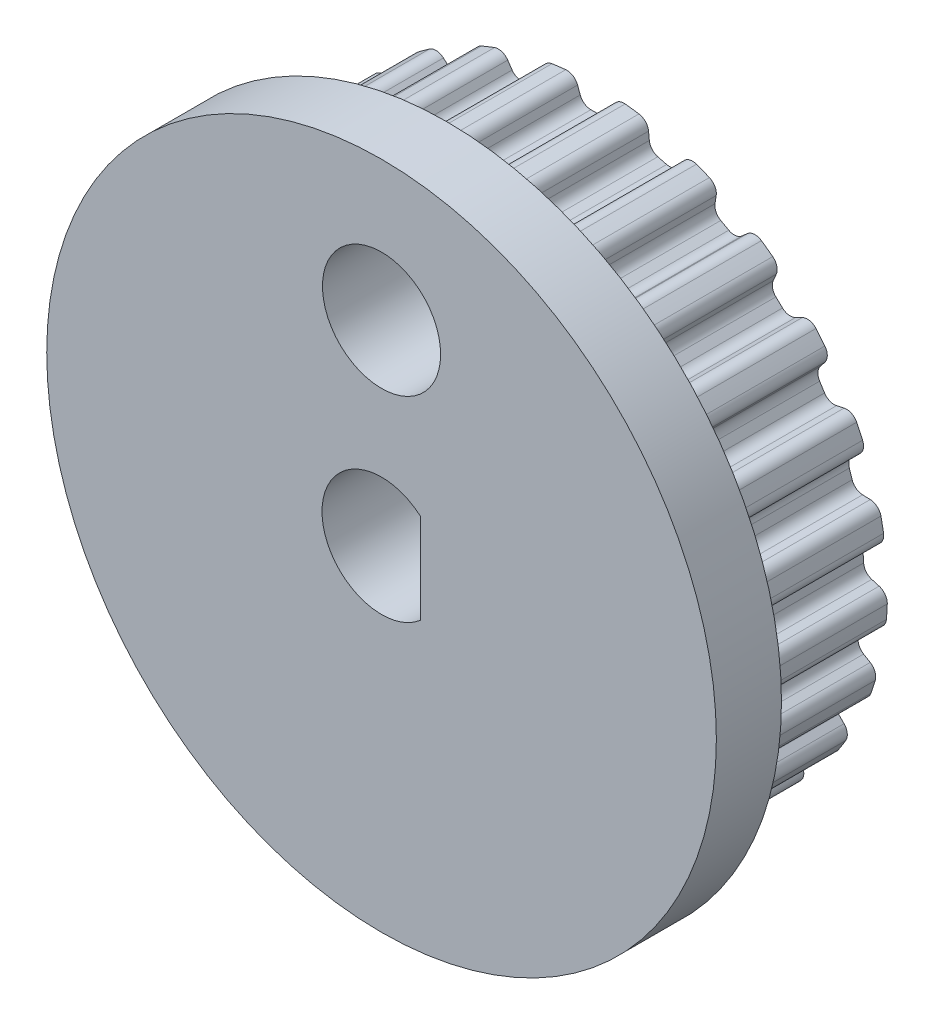
SolidWorks part; units mm, degrees
ref_plane "Front Plane" through (0, 0, 0) normal (0, 0, 1) x (1, 0, 0)
ref_plane "Top Plane" through (0, 0, 0) normal (0, 1, 0) x (1, 0, 0)
ref_plane "Right Plane" through (0, 0, 0) normal (1, 0, 0) x (0, 0, -1)
ref_plane "Plane1" through (0, 0, -5.3) normal (0, 0, -1) x (-1, 0, 0)
sketch "Sketch1" plane through (0, 0, -5.3) normal (0, 0, -1) x (-1, 0, 0)
  line L0 (-2.7705, -6.663) -> (-2.5415, -6.7537)
  line L1 (-2.3491, -7.0456) -> (-2.3549, -7.2528)
  line L2 (-1.4305, -7.4901) -> (-1.3357, -7.3057)
  line L3 (-1.0264, -7.1427) -> (-0.7821, -7.1735)
  line L4 (-0.5231, -7.4084) -> (-0.4772, -7.6106)
  line L5 (0.4772, -7.6106) -> (0.5231, -7.4084)
  line L6 (0.7821, -7.1735) -> (1.0264, -7.1427)
  line L7 (1.3357, -7.3057) -> (1.4305, -7.4901)
  line L8 (2.3549, -7.2528) -> (2.3491, -7.0456)
  line L9 (2.5415, -6.7537) -> (2.7705, -6.663)
  line L10 (3.1106, -6.744) -> (3.2483, -6.8991)
  line L11 (4.0846, -6.4393) -> (4.0274, -6.24)
  line L12 (4.1413, -5.9094) -> (4.3405, -5.7647)
  line L13 (4.6901, -5.7586) -> (4.862, -5.8745)
  line L14 (5.5576, -5.2212) -> (5.4527, -5.0424)
  line L15 (5.4808, -4.6939) -> (5.6377, -4.5041)
  line L16 (5.9748, -4.4113) -> (6.1701, -4.4808)
  line L17 (6.6815, -3.6751) -> (6.5354, -3.528)
  line L18 (6.4759, -3.1834) -> (6.5808, -2.9606)
  line L19 (6.8842, -2.7868) -> (7.0906, -2.8056)
  line L20 (7.3855, -1.898) -> (7.2075, -1.7918)
  line L21 (7.0641, -1.4729) -> (7.1103, -1.231)
  line L22 (7.3609, -0.9872) -> (7.5656, -0.9541)
  line L23 (7.6255, -0.0016) -> (7.4266, 0.0569)
  line L24 (7.2085, 0.3301) -> (7.193, 0.5759)
  line L25 (7.3752, 0.8744) -> (7.5652, 0.9574)
  line L26 (7.3864, 1.8948) -> (7.1792, 1.902)
  line L27 (6.8999, 2.1125) -> (6.8238, 2.3467)
  line L28 (6.9261, 2.681) -> (7.0894, 2.8087)
  line L29 (6.6831, 3.6722) -> (6.4806, 3.6277)
  line L30 (6.1578, 3.762) -> (6.0259, 3.9699)
  line L31 (6.0417, 4.3192) -> (6.1682, 4.4835)
  line L32 (5.5599, 5.2188) -> (5.3748, 5.1254)
  line L33 (5.0288, 5.1752) -> (4.8493, 5.3438)
  line L34 (4.7777, 5.6861) -> (4.8594, 5.8766)
  line L35 (4.0874, 6.4376) -> (3.9314, 6.301)
  line L36 (3.5837, 6.2632) -> (3.368, 6.3819)
  line L37 (3.2136, 6.6956) -> (3.2453, 6.9005)
  line L38 (2.358, 7.2518) -> (2.2409, 7.0807)
  line L39 (1.9136, 6.9577) -> (1.675, 7.0189)
  line L40 (1.4475, 7.2844) -> (1.4273, 7.4908)
  line L41 (0.4805, 7.6104) -> (0.4095, 7.4156)
  line L42 (0.1231, 7.215) -> (-0.1231, 7.215)
  line L43 (-0.4095, 7.4156) -> (-0.4805, 7.6104)
  line L44 (-1.4273, 7.4908) -> (-1.4475, 7.2844)
  line L45 (-1.675, 7.0189) -> (-1.9136, 6.9577)
  line L46 (-2.2409, 7.0807) -> (-2.358, 7.2518)
  line L47 (-3.2453, 6.9005) -> (-3.2136, 6.6956)
  line L48 (-3.368, 6.3819) -> (-3.5837, 6.2632)
  line L49 (-3.9314, 6.301) -> (-4.0874, 6.4376)
  line L50 (-4.8594, 5.8766) -> (-4.7777, 5.6861)
  line L51 (-4.8493, 5.3438) -> (-5.0288, 5.1752)
  line L52 (-5.3748, 5.1254) -> (-5.5599, 5.2188)
  line L53 (-6.1682, 4.4835) -> (-6.0417, 4.3192)
  line L54 (-6.0259, 3.9699) -> (-6.1578, 3.762)
  line L55 (-6.4806, 3.6277) -> (-6.6831, 3.6722)
  line L56 (-7.0894, 2.8087) -> (-6.9261, 2.681)
  line L57 (-6.8238, 2.3467) -> (-6.8999, 2.1125)
  line L58 (-7.1792, 1.902) -> (-7.3864, 1.8948)
  line L59 (-7.5652, 0.9574) -> (-7.3752, 0.8744)
  line L60 (-7.193, 0.5759) -> (-7.2085, 0.3301)
  line L61 (-7.4266, 0.0569) -> (-7.6255, -0.0016)
  line L62 (-7.5656, -0.9541) -> (-7.3609, -0.9872)
  line L63 (-7.1103, -1.231) -> (-7.0641, -1.4729)
  line L64 (-7.2075, -1.7918) -> (-7.3855, -1.898)
  line L65 (-7.0906, -2.8056) -> (-6.8842, -2.7868)
  line L66 (-6.5808, -2.9606) -> (-6.4759, -3.1834)
  line L67 (-6.5354, -3.528) -> (-6.6815, -3.6751)
  line L68 (-6.1701, -4.4808) -> (-5.9748, -4.4113)
  line L69 (-5.6377, -4.5041) -> (-5.4808, -4.6939)
  line L70 (-5.4527, -5.0424) -> (-5.5576, -5.2212)
  line L71 (-4.862, -5.8745) -> (-4.6901, -5.7586)
  line L72 (-4.3405, -5.7647) -> (-4.1413, -5.9094)
  line L73 (-4.0274, -6.24) -> (-4.0846, -6.4393)
  line L74 (-3.2483, -6.8991) -> (-3.1106, -6.744)
  arc A2 (-2.5415, -6.7537) -> (-2.3491, -7.0456) centre (-2.6537, -7.0371) cw
  arc A3 (-2.3549, -7.2528) -> (-2.133, -7.5547) centre (-2.0502, -7.2613) ccw
  arc A4 (-2.133, -7.5547) -> (-1.7703, -7.6478) centre (0, 0) ccw
  arc A5 (-1.7703, -7.6478) -> (-1.4305, -7.4901) centre (-1.7016, -7.3508) ccw
  arc A6 (-1.3357, -7.3057) -> (-1.0264, -7.1427) centre (-1.0646, -7.4451) cw
  arc A7 (-0.7821, -7.1735) -> (-0.5231, -7.4084) centre (-0.8203, -7.4759) cw
  arc A8 (-0.4772, -7.6106) -> (-0.1872, -7.8478) centre (-0.1799, -7.5431) ccw
  arc A9 (-0.1872, -7.8478) -> (0.1872, -7.8478) centre (0, 0) ccw
  arc A10 (0.1872, -7.8478) -> (0.4772, -7.6106) centre (0.1799, -7.5431) ccw
  arc A11 (0.5231, -7.4084) -> (0.7821, -7.1735) centre (0.8203, -7.4759) cw
  arc A12 (1.0264, -7.1427) -> (1.3357, -7.3057) centre (1.0646, -7.4451) cw
  arc A13 (1.4305, -7.4901) -> (1.7703, -7.6478) centre (1.7016, -7.3508) ccw
  arc A14 (1.7703, -7.6478) -> (2.133, -7.5547) centre (0, 0) ccw
  arc A15 (2.133, -7.5547) -> (2.3549, -7.2528) centre (2.0502, -7.2613) ccw
  arc A16 (2.3491, -7.0456) -> (2.5415, -6.7537) centre (2.6537, -7.0371) cw
  arc A17 (2.7705, -6.663) -> (3.1106, -6.744) centre (2.8827, -6.9464) cw
  arc A18 (3.2483, -6.8991) -> (3.6166, -6.9672) centre (3.4762, -6.6967) ccw
  arc A19 (3.6166, -6.9672) -> (3.9447, -6.7869) centre (0, 0) ccw
  arc A20 (3.9447, -6.7869) -> (4.0846, -6.4393) centre (3.7916, -6.5233) ccw
  arc A21 (4.0274, -6.24) -> (4.1413, -5.9094) centre (4.3204, -6.156) cw
  arc A22 (4.3405, -5.7647) -> (4.6901, -5.7586) centre (4.5196, -6.0113) cw
  arc A23 (4.862, -5.8745) -> (5.2357, -5.8489) centre (5.0324, -5.6218) ccw
  arc A24 (5.2357, -5.8489) -> (5.5086, -5.5926) centre (0, 0) ccw
  arc A25 (5.5086, -5.5926) -> (5.5576, -5.2212) centre (5.2947, -5.3755) ccw
  arc A26 (5.4527, -5.0424) -> (5.4808, -4.6939) centre (5.7156, -4.8882) cw
  arc A27 (5.6377, -4.5041) -> (5.9748, -4.4113) centre (5.8726, -4.6984) cw
  arc A28 (6.1701, -4.4808) -> (6.5258, -4.3631) centre (6.2724, -4.1937) ccw
  arc A29 (6.5258, -4.3631) -> (6.7264, -4.047) centre (0, 0) ccw
  arc A30 (6.7264, -4.047) -> (6.6815, -3.6751) centre (6.4652, -3.8898) ccw
  arc A31 (6.5354, -3.528) -> (6.4759, -3.1834) centre (6.7517, -3.3132) cw
  arc A32 (6.5808, -2.9606) -> (6.8842, -2.7868) centre (6.8565, -3.0904) cw
  arc A33 (7.0906, -2.8056) -> (7.4058, -2.6031) centre (7.1183, -2.5021) ccw
  arc A34 (7.4058, -2.6031) -> (7.5215, -2.247) centre (0, 0) ccw
  arc A35 (7.5215, -2.247) -> (7.3855, -1.898) centre (7.2295, -2.1598) ccw
  arc A36 (7.2075, -1.7918) -> (7.0641, -1.4729) centre (7.3635, -1.53) cw
  arc A37 (7.1103, -1.231) -> (7.3609, -0.9872) centre (7.4097, -1.2881) cw
  arc A38 (7.5656, -0.9541) -> (7.8205, -0.6796) centre (7.5169, -0.6532) ccw
  arc A39 (7.8205, -0.6796) -> (7.844, -0.3059) centre (0, 0) ccw
  arc A40 (7.844, -0.3059) -> (7.6255, -0.0016) centre (7.5395, -0.294) ccw
  arc A41 (7.4266, 0.0569) -> (7.2085, 0.3301) centre (7.5127, 0.3493) cw
  arc A42 (7.193, 0.5759) -> (7.3752, 0.8744) centre (7.4972, 0.5951) cw
  arc A43 (7.5652, 0.9574) -> (7.7438, 1.2866) centre (7.4432, 1.2367) ccw
  arc A44 (7.7438, 1.2866) -> (7.6737, 1.6544) centre (0, 0) ccw
  arc A45 (7.6737, 1.6544) -> (7.3864, 1.8948) centre (7.3757, 1.5902) ccw
  arc A46 (7.1792, 1.902) -> (6.8999, 2.1125) centre (7.1898, 2.2066) cw
  arc A47 (6.8238, 2.3467) -> (6.9261, 2.681) centre (7.1137, 2.4408) cw
  arc A48 (7.0894, 2.8087) -> (7.1806, 3.172) centre (6.9018, 3.0489) ccw
  arc A49 (7.1806, 3.172) -> (7.0212, 3.5108) centre (0, 0) ccw
  arc A50 (7.0212, 3.5108) -> (6.6831, 3.6722) centre (6.7485, 3.3745) ccw
  arc A51 (6.4806, 3.6277) -> (6.1578, 3.762) centre (6.4152, 3.9254) cw
  arc A52 (6.0259, 3.9699) -> (6.0417, 4.3192) centre (6.2832, 4.1333) cw
  arc A53 (6.1682, 4.4835) -> (6.1661, 4.8581) centre (5.9267, 4.6695) ccw
  arc A54 (6.1661, 4.8581) -> (5.9275, 5.1466) centre (0, 0) ccw
  arc A55 (5.9275, 5.1466) -> (5.5599, 5.2188) centre (5.6973, 4.9468) ccw
  arc A56 (5.3748, 5.1254) -> (5.0288, 5.1752) centre (5.2374, 5.3974) cw
  arc A57 (4.8493, 5.3438) -> (4.7777, 5.6861) centre (5.0579, 5.566) cw
  arc A58 (4.8594, 5.8766) -> (4.7643, 6.2389) centre (4.5793, 5.9967) ccw
  arc A59 (4.7643, 6.2389) -> (4.4613, 6.459) centre (0, 0) ccw
  arc A60 (4.4613, 6.459) -> (4.0874, 6.4376) centre (4.2881, 6.2082) ccw
  arc A61 (3.9314, 6.301) -> (3.5837, 6.2632) centre (3.7306, 6.5303) cw
  arc A62 (3.368, 6.3819) -> (3.2136, 6.6956) centre (3.5148, 6.649) cw
  arc A63 (3.2453, 6.9005) -> (3.063, 7.2278) centre (2.9441, 6.9471) ccw
  arc A64 (3.063, 7.2278) -> (2.7149, 7.3656) centre (0, 0) ccw
  arc A65 (2.7149, 7.3656) -> (2.358, 7.2518) centre (2.6095, 7.0796) ccw
  arc A66 (2.2409, 7.0807) -> (1.9136, 6.9577) centre (1.9894, 7.2529) cw
  arc A67 (1.675, 7.0189) -> (1.4475, 7.2844) centre (1.7508, 7.3142) cw
  arc A68 (1.4273, 7.4908) -> (1.1693, 7.7624) centre (1.1239, 7.461) ccw
  arc A69 (1.1693, 7.7624) -> (0.7979, 7.8093) centre (0, 0) ccw
  arc A70 (0.7979, 7.8093) -> (0.4805, 7.6104) centre (0.7669, 7.5061) ccw
  arc A71 (0.4095, 7.4156) -> (0.1231, 7.215) centre (0.1231, 7.5198) cw
  arc A72 (-0.1231, 7.215) -> (-0.4095, 7.4156) centre (-0.1231, 7.5198) cw
  arc A73 (-0.4805, 7.6104) -> (-0.7979, 7.8093) centre (-0.7669, 7.5061) ccw
  arc A74 (-0.7979, 7.8093) -> (-1.1693, 7.7624) centre (0, 0) ccw
  arc A75 (-1.1693, 7.7624) -> (-1.4273, 7.4908) centre (-1.1239, 7.461) ccw
  arc A76 (-1.4475, 7.2844) -> (-1.675, 7.0189) centre (-1.7508, 7.3142) cw
  arc A77 (-1.9136, 6.9577) -> (-2.2409, 7.0807) centre (-1.9894, 7.2529) cw
  arc A78 (-2.358, 7.2518) -> (-2.7149, 7.3656) centre (-2.6095, 7.0796) ccw
  arc A79 (-2.7149, 7.3656) -> (-3.063, 7.2278) centre (0, 0) ccw
  arc A80 (-3.063, 7.2278) -> (-3.2453, 6.9005) centre (-2.9441, 6.9471) ccw
  arc A81 (-3.2136, 6.6956) -> (-3.368, 6.3819) centre (-3.5148, 6.649) cw
  arc A82 (-3.5837, 6.2632) -> (-3.9314, 6.301) centre (-3.7306, 6.5303) cw
  arc A83 (-4.0874, 6.4376) -> (-4.4613, 6.459) centre (-4.2881, 6.2082) ccw
  arc A84 (-4.4613, 6.459) -> (-4.7643, 6.2389) centre (0, 0) ccw
  arc A85 (-4.7643, 6.2389) -> (-4.8594, 5.8766) centre (-4.5793, 5.9967) ccw
  arc A86 (-4.7777, 5.6861) -> (-4.8493, 5.3438) centre (-5.0579, 5.566) cw
  arc A87 (-5.0288, 5.1752) -> (-5.3748, 5.1254) centre (-5.2374, 5.3974) cw
  arc A88 (-5.5599, 5.2188) -> (-5.9275, 5.1466) centre (-5.6973, 4.9468) ccw
  arc A89 (-5.9275, 5.1466) -> (-6.1661, 4.8581) centre (0, 0) ccw
  arc A90 (-6.1661, 4.8581) -> (-6.1682, 4.4835) centre (-5.9267, 4.6695) ccw
  arc A91 (-6.0417, 4.3192) -> (-6.0259, 3.9699) centre (-6.2832, 4.1333) cw
  arc A92 (-6.1578, 3.762) -> (-6.4806, 3.6277) centre (-6.4152, 3.9254) cw
  arc A93 (-6.6831, 3.6722) -> (-7.0212, 3.5108) centre (-6.7485, 3.3745) ccw
  arc A94 (-7.0212, 3.5108) -> (-7.1806, 3.172) centre (0, 0) ccw
  arc A95 (-7.1806, 3.172) -> (-7.0894, 2.8087) centre (-6.9018, 3.0489) ccw
  arc A96 (-6.9261, 2.681) -> (-6.8238, 2.3467) centre (-7.1137, 2.4408) cw
  arc A97 (-6.8999, 2.1125) -> (-7.1792, 1.902) centre (-7.1898, 2.2066) cw
  arc A98 (-7.3864, 1.8948) -> (-7.6737, 1.6544) centre (-7.3757, 1.5902) ccw
  arc A99 (-7.6737, 1.6544) -> (-7.7438, 1.2866) centre (0, 0) ccw
  arc A100 (-7.7438, 1.2866) -> (-7.5652, 0.9574) centre (-7.4432, 1.2367) ccw
  arc A101 (-7.3752, 0.8744) -> (-7.193, 0.5759) centre (-7.4972, 0.5951) cw
  arc A102 (-7.2085, 0.3301) -> (-7.4266, 0.0569) centre (-7.5127, 0.3493) cw
  arc A103 (-7.6255, -0.0016) -> (-7.844, -0.3059) centre (-7.5395, -0.294) ccw
  arc A104 (-7.844, -0.3059) -> (-7.8205, -0.6796) centre (0, 0) ccw
  arc A105 (-7.8205, -0.6796) -> (-7.5656, -0.9541) centre (-7.5169, -0.6532) ccw
  arc A106 (-7.3609, -0.9872) -> (-7.1103, -1.231) centre (-7.4097, -1.2881) cw
  arc A107 (-7.0641, -1.4729) -> (-7.2075, -1.7918) centre (-7.3635, -1.53) cw
  arc A108 (-7.3855, -1.898) -> (-7.5215, -2.247) centre (-7.2295, -2.1598) ccw
  arc A109 (-7.5215, -2.247) -> (-7.4058, -2.6031) centre (0, 0) ccw
  arc A110 (-7.4058, -2.6031) -> (-7.0906, -2.8056) centre (-7.1183, -2.5021) ccw
  arc A111 (-6.8842, -2.7868) -> (-6.5808, -2.9606) centre (-6.8565, -3.0904) cw
  arc A112 (-6.4759, -3.1834) -> (-6.5354, -3.528) centre (-6.7517, -3.3132) cw
  arc A113 (-6.6815, -3.6751) -> (-6.7264, -4.047) centre (-6.4652, -3.8898) ccw
  arc A114 (-6.7264, -4.047) -> (-6.5258, -4.3631) centre (0, 0) ccw
  arc A115 (-6.5258, -4.3631) -> (-6.1701, -4.4808) centre (-6.2724, -4.1937) ccw
  arc A116 (-5.9748, -4.4113) -> (-5.6377, -4.5041) centre (-5.8726, -4.6984) cw
  arc A117 (-5.4808, -4.6939) -> (-5.4527, -5.0424) centre (-5.7156, -4.8882) cw
  arc A118 (-5.5576, -5.2212) -> (-5.5086, -5.5926) centre (-5.2947, -5.3755) ccw
  arc A119 (-5.5086, -5.5926) -> (-5.2357, -5.8489) centre (0, 0) ccw
  arc A120 (-5.2357, -5.8489) -> (-4.862, -5.8745) centre (-5.0324, -5.6218) ccw
  arc A121 (-4.6901, -5.7586) -> (-4.3405, -5.7647) centre (-4.5196, -6.0113) cw
  arc A122 (-4.1413, -5.9094) -> (-4.0274, -6.24) centre (-4.3204, -6.156) cw
  arc A123 (-4.0846, -6.4393) -> (-3.9447, -6.7869) centre (-3.7916, -6.5233) ccw
  arc A124 (-3.9447, -6.7869) -> (-3.6166, -6.9672) centre (0, 0) ccw
  arc A125 (-3.6166, -6.9672) -> (-3.2483, -6.8991) centre (-3.4762, -6.6967) ccw
  arc A126 (-3.1106, -6.744) -> (-2.7705, -6.663) centre (-2.8827, -6.9464) cw
extrude "Boss-Extrude1" add sketch "Sketch1" against normal blind 4
sketch "Sketch2" plane through (0, 0, -1.3) normal (0, 0, 1) x (1, 0, 0)
  circle A0 centre (0, 0) radius 9
extrude "Boss-Extrude2" add sketch "Sketch2" along normal blind 1.75
sketch "Sketch3" plane through (0, 0, 0.45) normal (0, 0, 1) x (1, 0, 0)
  line L0 (1.0416, 1.2145) -> (1.0416, -1.2145)
  arc A0 (1.0416, 1.2145) -> (1.0416, -1.2145) centre (0, 0) ccw
sketch "Sketch4" plane through (0, 0, -5.3) normal (0, 0, -1) x (-1, 0, 0)
  line L1 (-2.25, -2.25) -> (2.25, -2.25)
  line L2 (-2.25, -2.25) -> (-2.25, 2.25)
  line L3 (-2.25, 2.25) -> (2.25, 2.25)
  line L4 (2.25, -2.25) -> (2.25, 2.25)
  line L5 (-2.25, -2.25) -> (2.25, 2.25) construction
  line L6 (-2.25, 2.25) -> (2.25, -2.25) construction
  point P0 (0, 0)
  dimension "D1" = 4.5
  dimension "D2" = 4.5
extrude "Boss-Extrude3" add sketch "Sketch4" along normal blind 1.75
extrude "Cut-Extrude2" cut sketch "Sketch3" against normal through all
sketch "Sketch5" plane through (0, 0, 0.45) normal (0, 0, 1) x (1, 0, 0)
  circle A0 centre (0, 5.25) radius 1.5875
extrude "Cut-Extrude3" cut sketch "Sketch5" against normal through all
